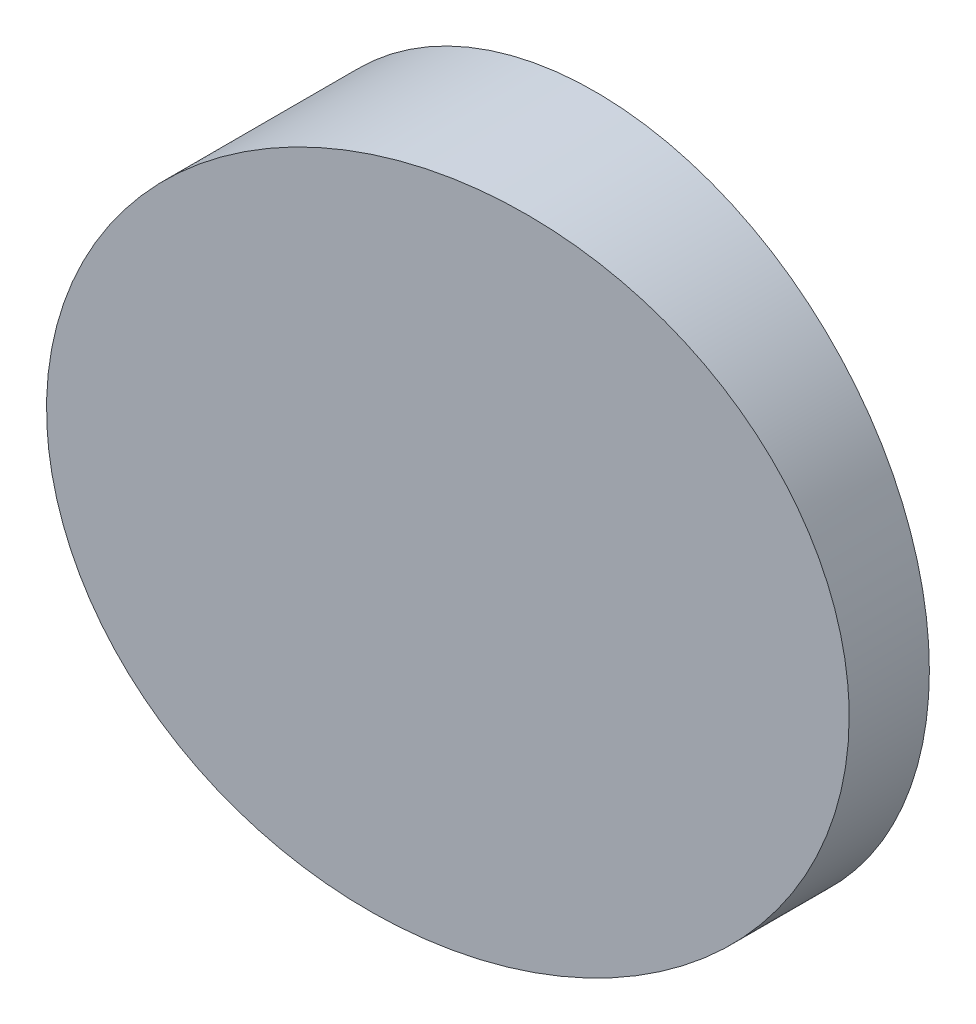
SolidWorks part; units mm, degrees
ref_plane "前视基准面" through (0, 0, 0) normal (0, 0, 1) x (1, 0, 0)
ref_plane "上视基准面" through (0, 0, 0) normal (0, 1, 0) x (1, 0, 0)
ref_plane "右视基准面" through (0, 0, 0) normal (1, 0, 0) x (0, 0, -1)
sketch "草图1" plane through (0, 0, 0) normal (0, 0, 1) x (1, 0, 0)
  circle A0 centre (0, 0) radius 12.5
extrude "凸台-拉伸1" add sketch "草图1" along normal blind 10
sketch "草图2" plane through (0, 0, 0) normal (0, 1, 0) x (1, 0, 0)
  line L0 (12.5, -3) -> (-16.0722, -8.7352)
  line L1 (12.5, -10) -> (12.5, 0) construction
  line L2 (-16.0722, -8.7352) -> (-16.0722, -19.6731)
  line L3 (-16.0722, -19.6731) -> (18.3366, -19.6731)
  line L4 (18.3366, -19.6731) -> (18.3366, -3)
  line L5 (18.3366, -3) -> (12.5, -3)
  line L6 (12.5, 0) -> (-12.5, 0) construction
  dimension "D1" = 11.35
  dimension "D2" = 3
extrude "切除-拉伸1" cut sketch "草图2" against normal mid plane 50
